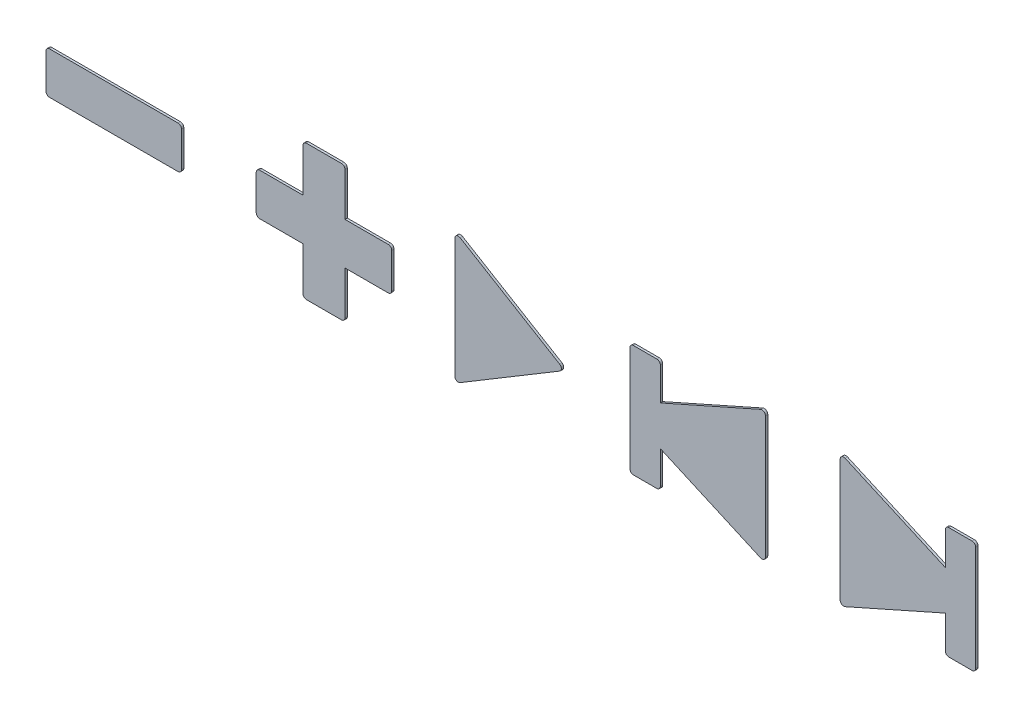
SolidWorks part; units mm, degrees
ref_plane "Front Plane" through (0, 0, 0) normal (0, 0, 1) x (1, 0, 0)
ref_plane "Top Plane" through (0, 0, 0) normal (0, 1, 0) x (1, 0, 0)
ref_plane "Right Plane" through (0, 0, 0) normal (1, 0, 0) x (0, 0, -1)
sketch "Sketch1" plane through (0, 0, 0) normal (0, 0, 1) x (1, 0, 0)
  line L1 (-61, 40) -> (61, 40)
  line L2 (-63, 38) -> (-63, -38)
  line L3 (-61, -40) -> (61, -40)
  line L4 (63, 38) -> (63, -38)
  line L5 (-63, 40) -> (63, -40) construction
  line L6 (-63, -40) -> (63, 40) construction
  arc A0 (61, 40) -> (63, 38) centre (61, 38) cw
  arc A1 (63, -38) -> (61, -40) centre (61, -38) cw
  arc A2 (-61, -40) -> (-63, -38) centre (-61, -38) cw
  arc A3 (-63, 38) -> (-61, 40) centre (-61, 38) cw
  point P0 (0, 0)
  dimension "D1" = 2
sketch "Sketch2" plane through (0, 0, 0) normal (0, 0, 1) x (1, 0, 0)
  line L35 (-4.8, 5.1169) -> (-4.8, -5.1169)
  line L36 (-4.3457, -5.3742) -> (4.1825, -0.2572)
  line L37 (4.1825, 0.2572) -> (-4.3457, 5.3742)
  line L38 (-10.2, -1.5) -> (-10.2, 1.5)
  line L39 (-10.5, 1.8) -> (-14.2, 1.8)
  line L40 (-14.2, 1.8) -> (-14.2, 5.5)
  line L41 (-14.5, 5.8) -> (-17.5, 5.8)
  line L42 (-17.8, 5.5) -> (-17.8, 1.8)
  line L43 (-17.8, 1.8) -> (-21.5, 1.8)
  line L44 (-21.8, 1.5) -> (-21.8, -1.5)
  line L45 (-21.5, -1.8) -> (-17.8, -1.8)
  line L46 (-17.8, -1.8) -> (-17.8, -5.5)
  line L47 (-17.5, -5.8) -> (-14.5, -5.8)
  line L48 (-14.2, -5.5) -> (-14.2, -1.8)
  line L49 (-14.2, -1.8) -> (-10.5, -1.8)
  line L50 (-28.2, 1.5) -> (-28.2, -1.5)
  line L51 (-28.5, -1.8) -> (-39.5, -1.8)
  line L52 (-39.8, -1.5) -> (-39.8, 1.5)
  line L53 (-39.5, 1.8) -> (-28.5, 1.8)
  line L54 (10.2, 4.5) -> (10.2, -4.5)
  line L55 (10.5, -4.8) -> (12.5, -4.8)
  line L56 (12.8, -4.5) -> (12.8, -1.6922)
  line L57 (12.8, -1.6922) -> (21.3782, -5.5048)
  line L58 (21.8, -5.2306) -> (21.8, 5.2306)
  line L59 (21.3782, 5.5048) -> (12.8, 1.6922)
  line L60 (12.8, 1.6922) -> (12.8, 4.5)
  line L61 (12.5, 4.8) -> (10.5, 4.8)
  line L62 (28.2, 5.2306) -> (28.2, -5.2306)
  line L63 (28.6218, -5.5048) -> (37.2, -1.6922)
  line L64 (37.2, -4.5) -> (37.2, -1.6922)
  line L65 (39.5, -4.8) -> (37.5, -4.8)
  line L66 (39.8, 4.5) -> (39.8, -4.5)
  line L67 (37.5, 4.8) -> (39.5, 4.8)
  line L68 (37.2, 1.6922) -> (37.2, 4.5)
  line L69 (28.6218, 5.5048) -> (37.2, 1.6922)
  arc A27 (-4.3457, -5.3742) -> (-4.8, -5.1169) centre (-4.5, -5.1169) cw
  arc A28 (4.1825, -0.2572) -> (4.1825, 0.2572) centre (4.0282, 0) ccw
  arc A29 (-4.8, 5.1169) -> (-4.3457, 5.3742) centre (-4.5, 5.1169) cw
  arc A30 (-10.5, 1.8) -> (-10.2, 1.5) centre (-10.5, 1.5) cw
  arc A31 (-14.5, 5.8) -> (-14.2, 5.5) centre (-14.5, 5.5) cw
  arc A32 (-17.8, 5.5) -> (-17.5, 5.8) centre (-17.5, 5.5) cw
  arc A33 (-21.8, 1.5) -> (-21.5, 1.8) centre (-21.5, 1.5) cw
  arc A34 (-21.5, -1.8) -> (-21.8, -1.5) centre (-21.5, -1.5) cw
  arc A35 (-17.5, -5.8) -> (-17.8, -5.5) centre (-17.5, -5.5) cw
  arc A36 (-14.5, -5.8) -> (-14.2, -5.5) centre (-14.5, -5.5) ccw
  arc A37 (-10.5, -1.8) -> (-10.2, -1.5) centre (-10.5, -1.5) ccw
  arc A38 (-28.2, -1.5) -> (-28.5, -1.8) centre (-28.5, -1.5) cw
  arc A39 (-39.5, -1.8) -> (-39.8, -1.5) centre (-39.5, -1.5) cw
  arc A40 (-39.8, 1.5) -> (-39.5, 1.8) centre (-39.5, 1.5) cw
  arc A41 (-28.5, 1.8) -> (-28.2, 1.5) centre (-28.5, 1.5) cw
  arc A42 (10.5, -4.8) -> (10.2, -4.5) centre (10.5, -4.5) cw
  arc A43 (12.5, -4.8) -> (12.8, -4.5) centre (12.5, -4.5) ccw
  arc A44 (21.8, -5.2306) -> (21.3782, -5.5048) centre (21.5, -5.2306) cw
  arc A45 (21.3782, 5.5048) -> (21.8, 5.2306) centre (21.5, 5.2306) cw
  arc A46 (12.5, 4.8) -> (12.8, 4.5) centre (12.5, 4.5) cw
  arc A47 (10.2, 4.5) -> (10.5, 4.8) centre (10.5, 4.5) cw
  arc A48 (28.6218, -5.5048) -> (28.2, -5.2306) centre (28.5, -5.2306) cw
  arc A49 (37.5, -4.8) -> (37.2, -4.5) centre (37.5, -4.5) cw
  arc A50 (39.5, -4.8) -> (39.8, -4.5) centre (39.5, -4.5) ccw
  arc A51 (39.8, 4.5) -> (39.5, 4.8) centre (39.5, 4.5) ccw
  arc A52 (37.2, 4.5) -> (37.5, 4.8) centre (37.5, 4.5) cw
  arc A53 (28.2, 5.2306) -> (28.6218, 5.5048) centre (28.5, 5.2306) cw
extrude "Boss-Extrude1" add sketch "Sketch2" along normal blind 0.2
